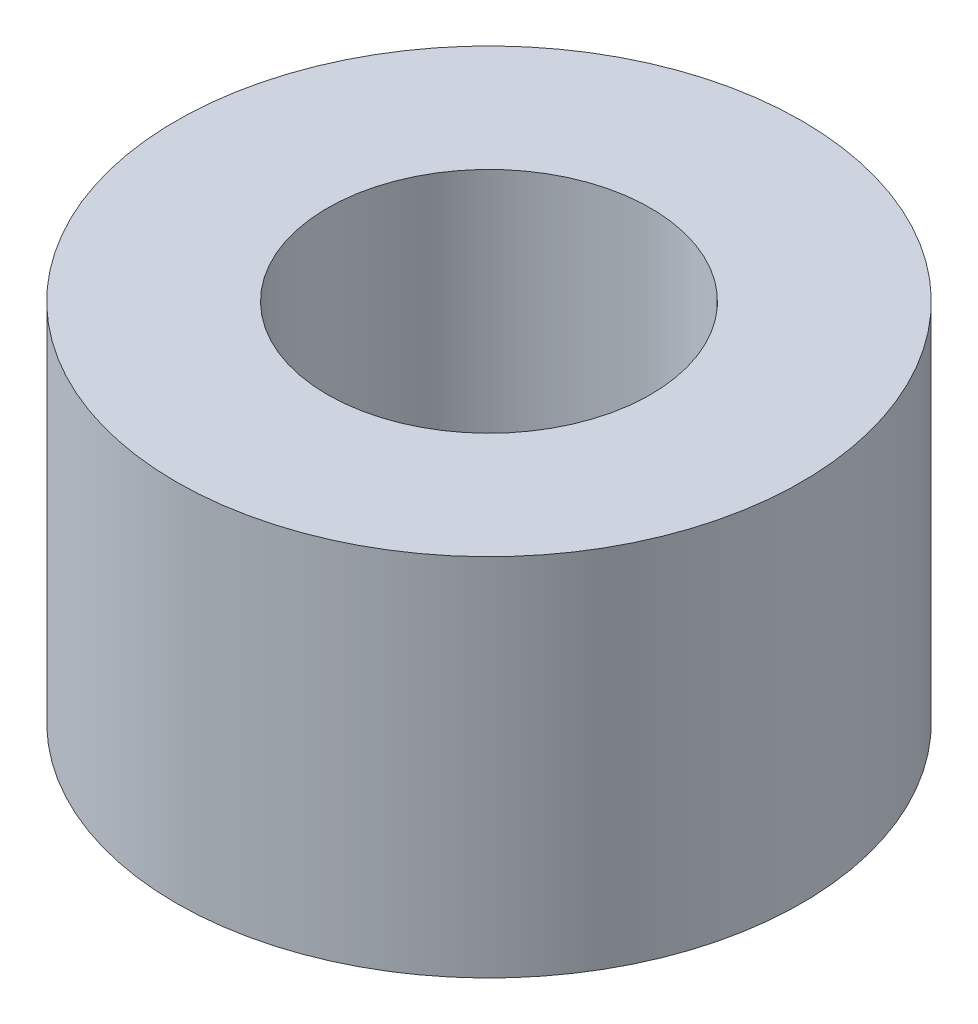
SolidWorks part; units mm, degrees
material "6061 合金"
ref_plane "前视基准面" through (0, 0, 0) normal (0, 0, 1) x (1, 0, 0)
ref_plane "上视基准面" through (0, 0, 0) normal (0, 1, 0) x (1, 0, 0)
ref_plane "右视基准面" through (0, 0, 0) normal (1, 0, 0) x (0, 0, -1)
sketch "草图1" plane through (0, 0, 0) normal (0, 1, 0) x (1, 0, 0)
  circle A0 centre (0, 0) radius 1.55
  circle A1 centre (0, 0) radius 3
  dimension "D1" = 6
  dimension "D2" = 3.1
extrude "凸台-拉伸1" add sketch "草图1" along normal blind 3.5
